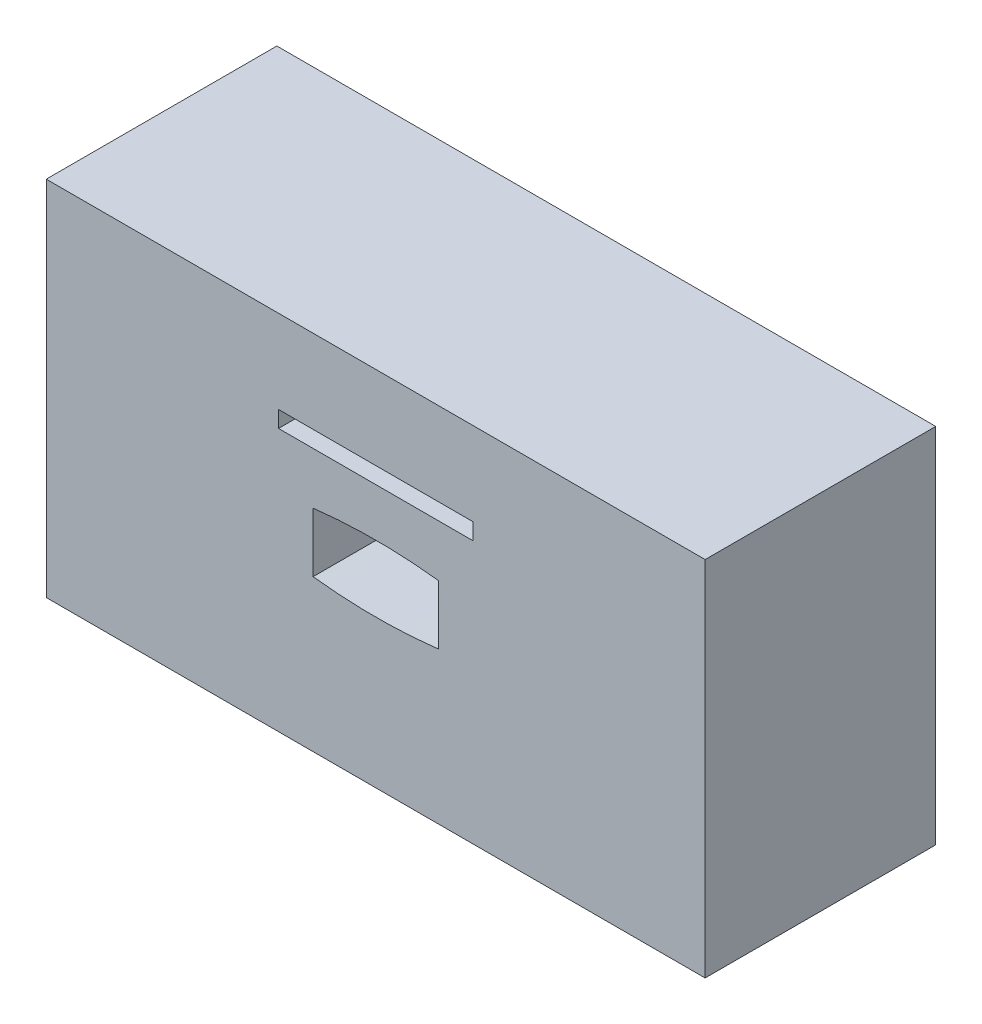
SolidWorks part; units mm, degrees
ref_plane "Plan de face" through (0, 0, 0) normal (0, 0, 1) x (1, 0, 0)
ref_plane "Plan de dessus" through (0, 0, 0) normal (0, 1, 0) x (1, 0, 0)
ref_plane "Plan de droite" through (0, 0, 0) normal (1, 0, 0) x (0, 0, -1)
sketch "Esquisse1" plane through (0, 0, 0) normal (0, 0, 1) x (1, 0, 0)
  line L1 (-50, 27.5) -> (50, 27.5)
  line L2 (-50, 27.5) -> (-50, -27.5)
  line L3 (-50, -27.5) -> (50, -27.5)
  line L4 (50, 27.5) -> (50, -27.5)
  line L5 (-50, 27.5) -> (50, -27.5) construction
  line L6 (-50, -27.5) -> (50, 27.5) construction
  point P0 (0, 0)
  dimension "D1" = 100
  dimension "D2" = 55
extrude "Boss.-Extru.1" add sketch "Esquisse1" along normal blind 35
sketch "Esquisse2" plane through (0, 0, 35) normal (0, 0, 1) x (1, 0, 0)
  line L0 (-9.5, 0) -> (9.5, 0) construction
  line L1 (-9.5, 4.5) -> (-9.5, -4.5)
  line L2 (0, -19.25) -> (0, 19.25) construction
  line L3 (9.5, 4.5) -> (9.5, -4.5)
  line L4 (19.25, 0) -> (-19.25, 0) construction
  line L8 (-14.75, 14.8576) -> (14.75, 14.8576)
  line L9 (-14.75, 14.8576) -> (-14.75, 12.3576)
  line L10 (-14.75, 12.3576) -> (14.75, 12.3576)
  line L11 (14.75, 14.8576) -> (14.75, 12.3576)
  line L12 (-14.75, 14.8576) -> (14.75, 12.3576) construction
  line L13 (-14.75, 12.3576) -> (14.75, 14.8576) construction
  arc A0 (-9.5, 4.5) -> (9.5, 4.5) centre (0, -75.201) cw
  arc A1 (-9.5, -4.5) -> (9.5, -4.5) centre (0, 75.201) ccw
  point P2 (0, 0)
  point P7 (-9.5, 0)
  point P22 (0, 13.6076)
  point P27 (0, 0)
  dimension "D1" = 9
  dimension "D2" = 2.5
  dimension "D3" = 29.5
  dimension "D4" = 19
extrude "Enlèv. mat.-Extru.1" cut sketch "Esquisse2" against normal blind 20
